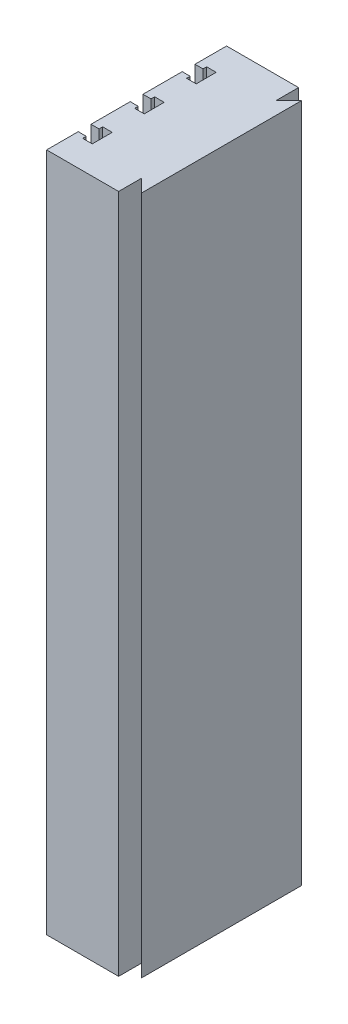
SolidWorks part; units mm, degrees
ref_plane "Front Plane" through (0, 0, 0) normal (0, 0, 1) x (1, 0, 0)
ref_plane "Top Plane" through (0, 0, 0) normal (0, 1, 0) x (1, 0, 0)
ref_plane "Right Plane" through (0, 0, 0) normal (1, 0, 0) x (0, 0, -1)
sketch "Sketch1" plane through (0, 0, 0) normal (0, 1, 0) x (1, 0, 0)
  line L0 (-53, 0) -> (133.5772, 0) construction
  line L1 (-53, -112.5) -> (53, -112.5)
  line L2 (-53, -112.5) -> (-53, 112.5)
  line L3 (-53, 112.5) -> (53, 112.5)
  line L4 (53, -112.5) -> (53, 112.5)
  line L5 (-53, -112.5) -> (53, 112.5) construction
  line L6 (-53, 112.5) -> (53, -112.5) construction
  line L7 (-53, -65) -> (81.727, -65) construction
  line L8 (-53, 65) -> (81.727, 65) construction
  line L9 (-43, 73) -> (-43, 77.5)
  line L10 (-53, 73) -> (-43, 73)
  line L11 (-53, 73) -> (-53, 57)
  line L12 (-53, 57) -> (-43, 57)
  line L14 (-43, 52.5) -> (-31, 52.5)
  line L15 (-43, 52.5) -> (-43, 57)
  line L16 (-43, 77.5) -> (-31, 77.5)
  line L17 (-31, 52.5) -> (-31, 77.5)
  line L18 (-43, 52.5) -> (-31, 77.5) construction
  line L19 (-43, 77.5) -> (-31, 52.5) construction
  line L20 (-53, -73) -> (-43, -73)
  line L21 (-43, -73) -> (-43, -77.5)
  line L22 (-43, -77.5) -> (-31, -77.5)
  line L23 (-31, -52.5) -> (-31, -77.5)
  line L24 (-43, -52.5) -> (-31, -52.5)
  line L25 (-43, -52.5) -> (-43, -57)
  line L26 (-53, -57) -> (-43, -57)
  line L27 (-53, -73) -> (-53, -57)
  line L28 (-53, -32.5) -> (84.3953, -32.5) construction
  line L29 (-53, 8) -> (-53, -8)
  line L30 (-53, -8) -> (-43, -8)
  line L31 (-43, -12.5) -> (-43, -8)
  line L32 (-43, -12.5) -> (-31, -12.5)
  line L33 (-31, -12.5) -> (-31, 12.5)
  line L34 (-43, 12.5) -> (-31, 12.5)
  line L35 (-43, 8) -> (-43, 12.5)
  line L36 (-53, 8) -> (-43, 8)
  line L37 (53, 100) -> (37, 84)
  line L38 (37, 84) -> (37, 112.5)
  line L39 (37, -84) -> (37, -112.5)
  line L40 (53, -100) -> (37, -84)
  point P0 (0, 0)
  point P16 (-37, 65)
  dimension "D1" = 106
  dimension "D2" = 225
  dimension "D3" = 65
  dimension "D4" = 16
  dimension "D5" = 25
  dimension "D6" = 10
  dimension "D7" = 12
  dimension "D8" = 32.5
  dimension "D9" = 90
  dimension "D10" = 45
  dimension "D11" = 200
extrude "Boss-Extrude1" add sketch "Sketch1" along normal blind 850 contours L40 L4 L37 L38 L3 L2 L10 L9 L16 L17 L14 L15 L12 L36 L35 L34 L33 L32 L31 L30 L26 L25 L24 L23 L22 L21 L20 L1 L39
sketch "Sketch2" plane through (-53, 0, 0) normal (-1, 0, 0) x (0, 0, 1)
  line L0 (-82.5, 45) -> (82.5, 45) construction
  line L1 (-82.5, 65) -> (82.5, 65)
  line L2 (-82.5, 25) -> (82.5, 25)
  line L3 (-112.5, 425) -> (267.3278, 425) construction
  line L4 (-112.5, 850) -> (-112.5, 0) construction
  line L5 (-82.5, 805) -> (82.5, 805) construction
  line L6 (-82.5, 785) -> (82.5, 785)
  line L7 (-82.5, 825) -> (82.5, 825)
  line L8 (-8, 0) -> (-57, 0) construction
  arc A0 (-82.5, 65) -> (-82.5, 25) centre (-82.5, 45) ccw
  arc A1 (82.5, 25) -> (82.5, 65) centre (82.5, 45) ccw
  arc A2 (-82.5, 785) -> (-82.5, 825) centre (-82.5, 805) cw
  arc A3 (82.5, 825) -> (82.5, 785) centre (82.5, 805) cw
  point P2 (0, 45)
  point P13 (0, 805)
  point P20 (0, 0)
  dimension "D3" = 20
  dimension "D1" = 165
  dimension "D2" = 45
extrude "Cut-Extrude1" cut sketch "Sketch2" against normal up to surface (22 mm away) up to face at (-31, 425, 0)
